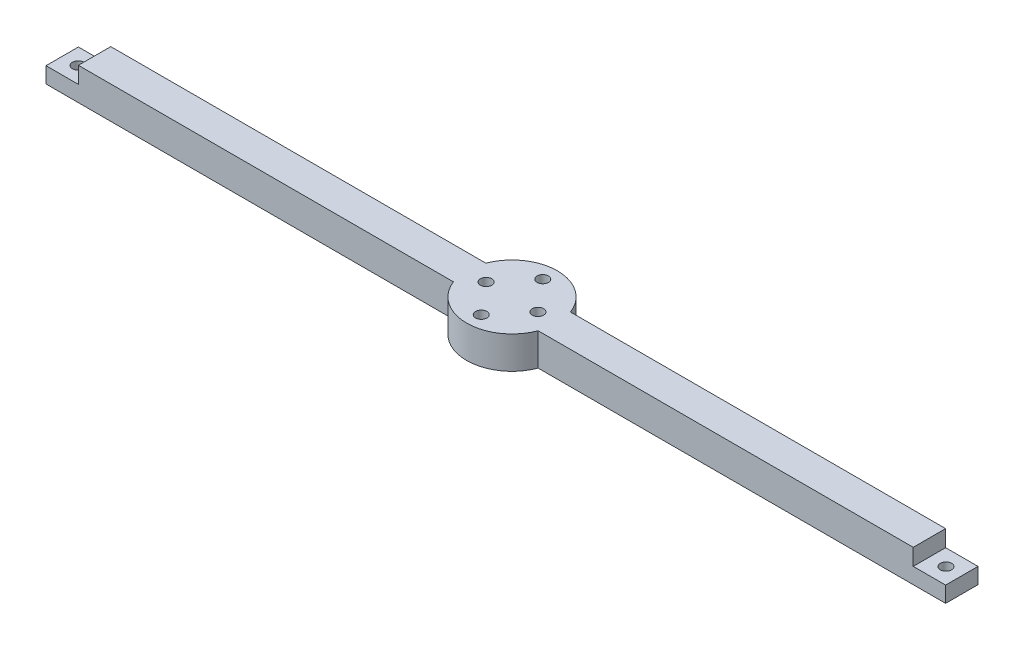
SolidWorks part; units mm, degrees
ref_plane "Front Plane" through (0, 0, 0) normal (0, 0, 1) x (1, 0, 0)
ref_plane "Top Plane" through (0, 0, 0) normal (0, 1, 0) x (1, 0, 0)
ref_plane "Right Plane" through (0, 0, 0) normal (1, 0, 0) x (0, 0, -1)
sketch "Sketch1" plane through (0, 0, 0) normal (0, 1, 0) x (1, 0, 0)
  circle A0 centre (0, 0) radius 14
  dimension "D1" = 28
extrude "Boss-Extrude1" add sketch "Sketch1" along normal blind 10
sketch "Sketch2" plane through (0, 10, 0) normal (0, 1, 0) x (1, 0, 0)
  line L0 (14, 0) -> (149, 0) construction
  line L1 (13.0767, -5) -> (149, -5)
  line L2 (13.0767, 5) -> (149, 5)
  line L4 (149, -5) -> (149, 5)
  line L5 (0, 5) -> (149, 5) construction
  line L6 (0, 0) -> (149, 0) construction
  line L7 (0, -5) -> (149, -5) construction
  circle A1 centre (0, 0) radius 14
  arc A2 (13.0767, -5) -> (13.0767, 5) centre (0, 0) ccw
  point P19 (0, 0)
  dimension "D1" = 149
  dimension "D2" = 5
  dimension "D3" = 5
  dimension "D4" = 0
extrude "Boss-Extrude2" add sketch "Sketch2" against normal up to surface (10 mm away) up to face at (0, 0, 14)
sketch "Sketch4" plane through (0, 0, 5) normal (0, 0, 1) x (1, 0, 0)
  line L0 (149, 0) -> (139, 0) construction
  line L1 (149, 0) -> (13.0767, 0) construction
  line L2 (139, 0) -> (139, 5) construction
  line L3 (139, 5) -> (129, 5) construction
  line L4 (129, 5) -> (129, 10) construction
  line L5 (13.0767, 10) -> (149, 10) construction
  line L6 (138.9, 0) -> (138.9, 4.9)
  line L7 (138.9, 4.9) -> (128.9, 4.9)
  line L8 (128.9, 4.9) -> (128.9, 10)
  line L9 (128.9, 10) -> (149, 10)
  line L10 (149, 10) -> (149, 0)
  line L11 (149, 0) -> (138.9, 0)
  dimension "D1" = 10
  dimension "D2" = 10
  dimension "D3" = 5
  dimension "D4" = 0.1
extrude "Cut-Extrude2" cut sketch "Sketch4" against normal through all
sketch "Sketch6" plane through (0, 4.9, 0) normal (0, 1, 0) x (1, 0, 0)
  line L0 (138.9, 5) -> (128.9, 5) construction
  line L1 (129, 5) -> (139, 5) construction
  line L2 (129, 5) -> (129, -5) construction
  line L3 (129, -5) -> (139, -5) construction
  line L4 (139, 5) -> (139, -5) construction
  line L5 (128.9, -5) -> (138.9, -5) construction
  line L6 (138.9, 5) -> (138.9, -5) construction
  line L7 (128.9, 5) -> (128.9, -5) construction
  line L8 (129, 5) -> (139, -5) construction
  circle A0 centre (134, 0) radius 1.75
  dimension "D3" = 3.5
  dimension "D1" = 0.1
  dimension "D2" = 0.1
extrude "Cut-Extrude4" cut sketch "Sketch6" against normal blind 10
pattern_circular "CirPattern2" count 2 over 180 about axis through (0, 0, 0) along (0, 1, 0) of "Boss-Extrude2", "Cut-Extrude2", "Cut-Extrude4"
sketch "Sketch5" plane through (0, 10, 0) normal (0, 1, 0) x (1, 0, 0)
  line L0 (-8, 0) -> (8, 0) construction
  line L1 (0, -9.5) -> (0, 9.5) construction
  circle A0 centre (0, 9.5) radius 1.75
  circle A1 centre (8, 0) radius 1.75
  circle A2 centre (-8, 0) radius 1.75
  circle A3 centre (0, -9.5) radius 1.75
  point P4 (0, 0)
  point P5 (0, 0)
  dimension "D3" = 3.5
  dimension "D1" = 16
  dimension "D2" = 19
extrude "Cut-Extrude3" cut sketch "Sketch5" against normal through all
sketch "Sketch8" plane through (0, 0, 0) normal (0, -1, 0) x (1, 0, 0)
  circle A0 centre (0, 0) radius 4.75
  dimension "D1" = 9.5
extrude "Cut-Extrude6" cut sketch "Sketch8" against normal blind 4
